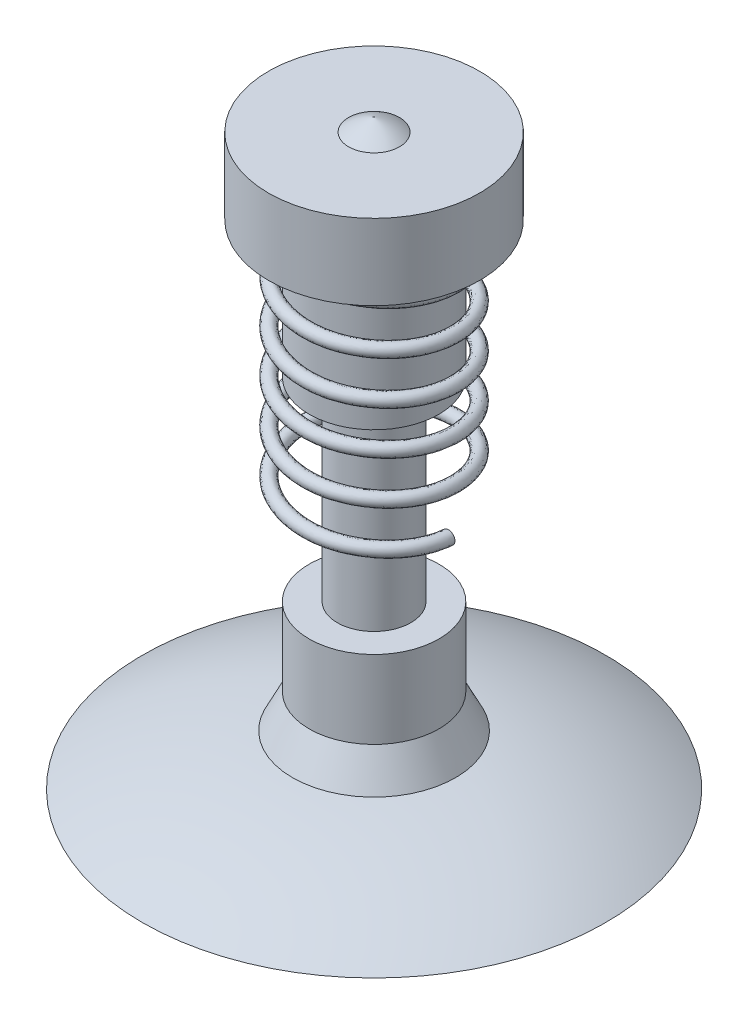
SolidWorks part; units mm, degrees
ref_plane "Front Plane" through (0, 0, 0) normal (0, 0, 1) x (1, 0, 0)
ref_plane "Top Plane" through (0, 0, 0) normal (0, 1, 0) x (1, 0, 0)
ref_plane "Right Plane" through (0, 0, 0) normal (1, 0, 0) x (0, 0, -1)
sketch "Sketch5" plane through (0, 0, 0) normal (0, 0, 1) x (1, 0, 0)
  line L0 (0, 2.69) -> (0, 0)
  line L1 (0, 0) -> (1.0712, 0)
  line L2 (0.3774, 0.2336) -> (0.3, 0.39)
  line L3 (0.3, 0.39) -> (0.3, 0.7502)
  line L4 (0.3, 0.7502) -> (0.17, 0.7502)
  line L5 (0.17, 0.7502) -> (0.17, 1.5608)
  line L6 (0.17, 1.5608) -> (0.3, 1.65)
  line L7 (0.3, 1.65) -> (0.3, 2.28)
  line L8 (0.3, 2.28) -> (0.4883, 2.28)
  line L9 (0.4883, 2.28) -> (0.4883, 2.63)
  line L10 (0.4883, 2.63) -> (0.1177, 2.63)
  arc A0 (1.0712, 0) -> (0.3774, 0.2336) centre (0.1673, -1.5374) ccw
  arc A1 (0.1177, 2.63) -> (0, 2.69) centre (-0.1184, 2.3126) ccw
  point P16 (0.3774, 0.2336)
  point P17 (0.17, 1.4793)
  point P18 (0, 0)
  point P19 (0.17, 1.5608)
  dimension "D1" = 2.69
  dimension "D2" = 1.0712
  dimension "D3" = 0.35
  dimension "D4" = 0.63
  dimension "D5" = 0.17
  dimension "D6" = 0.3
  dimension "D7" = 0.3
  dimension "D8" = 0.06
revolve "Revolve2" add sketch "Sketch5" angle 360 about L0
sketch "Sketch6" plane through (0, 2.28, 0) normal (0, -1, 0) x (1, 0, 0)
  circle A0 centre (0, 0) radius 0.344
  dimension "D1" = 0.688
curve "Helix/Spiral2" pitch 0.2 height 1.1 turns 5.5
sketch "Sketch7" plane through (0, 0, 0) normal (0, 0, 1) x (1, 0, 0)
  circle A0 centre (0.344, 2.18) radius 0.03
  point P2 (0, 0)
  dimension "D1" = 0.06
sweep "Sweep1" add profiles "Sketch7" path "Helix/Spiral2"
